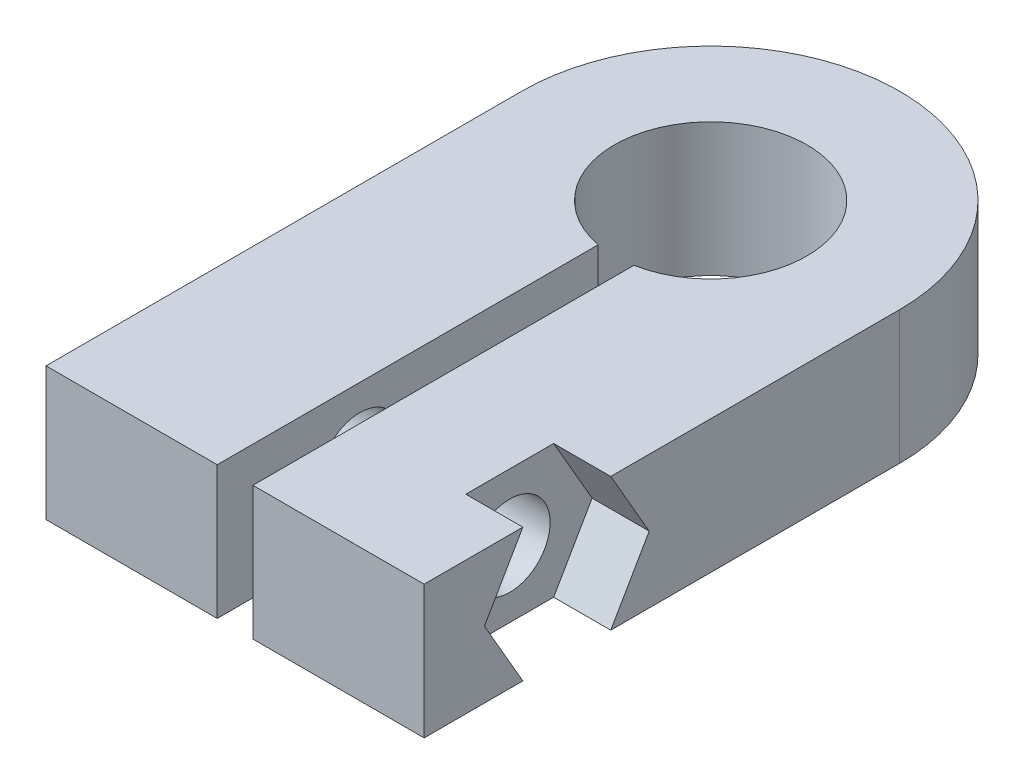
SolidWorks part; units mm, degrees
ref_plane "Front Plane" through (0, 0, 0) normal (0, 0, 1) x (1, 0, 0)
ref_plane "Top Plane" through (0, 0, 0) normal (0, 1, 0) x (1, 0, 0)
ref_plane "Right Plane" through (0, 0, 0) normal (1, 0, 0) x (0, 0, -1)
sketch "Sketch1" plane through (0, 0, 0) normal (0, 1, 0) x (1, 0, 0)
  line L0 (-7.95, -20) -> (-7.95, 0)
  line L1 (7.95, 0) -> (7.95, -20)
  line L2 (7.95, -20) -> (0.75, -20)
  line L3 (0.75, -20) -> (0.75, -3.9799)
  line L4 (-7.95, -20) -> (-0.75, -20)
  line L5 (-0.75, -20) -> (-0.75, -3.9799)
  arc A0 (-7.95, 0) -> (7.95, 0) centre (0, 0) cw
  arc A1 (-0.75, -3.9799) -> (0.75, -3.9799) centre (0, 0) cw
  dimension "D1" = 3.9
  dimension "D2" = 4.05
  dimension "D3" = 1.5
  dimension "D4" = 20
extrude "Boss-Extrude1" add sketch "Sketch1" along normal blind 5.6
sketch "Sketch2" plane through (-7.95, 0, 0) normal (-1, 0, 0) x (0, 0, 1)
  line L0 (20, 5.6) -> (20, 0) construction
  circle A0 centre (14, 2.8) radius 1.7
  point P4 (20, 2.8)
  dimension "D2" = 3.4
  dimension "D1" = 6
extrude "Cut-Extrude1" cut sketch "Sketch2" against normal through all
sketch "Sketch3" plane through (-7.95, 0, 0) normal (-1, 0, 0) x (0, 0, 1)
  circle A0 centre (14, 2.8) radius 2.5
  circle A1 centre (14, 2.8) radius 1.7 construction
  dimension "D1" = 5
sketch "Sketch4" plane through (7.95, 0, 0) normal (1, 0, 0) x (0, 0, -1)
  line L0 (-17.4641, 2.8) -> (-15.8475, 5.6)
  line L1 (-12.2679, -0.2) -> (-10.5359, 2.8) construction
  line L2 (-10.5359, 2.8) -> (-12.2679, 5.8) construction
  line L3 (-12.2679, 5.8) -> (-15.7321, 5.8) construction
  line L4 (-15.7321, 5.8) -> (-17.4641, 2.8) construction
  line L5 (-17.4641, 2.8) -> (-15.7321, -0.2) construction
  line L6 (-15.7321, -0.2) -> (-12.2679, -0.2) construction
  line L7 (-20, 5.6) -> (0, 5.6) construction
  line L8 (-15.8475, 5.6) -> (-12.1525, 5.6)
  line L9 (-12.1525, 5.6) -> (-10.5359, 2.8)
  line L10 (-10.5359, 2.8) -> (-12.1525, 0)
  line L11 (-20, 0) -> (0, 0) construction
  line L12 (-12.1525, 0) -> (-15.8475, 0)
  line L13 (-15.8475, 0) -> (-17.4641, 2.8)
  circle A0 centre (-14, 2.8) radius 3 construction
  dimension "D1" = 6
extrude "Cut-Extrude2" cut sketch "Sketch4" against normal blind 2.4
